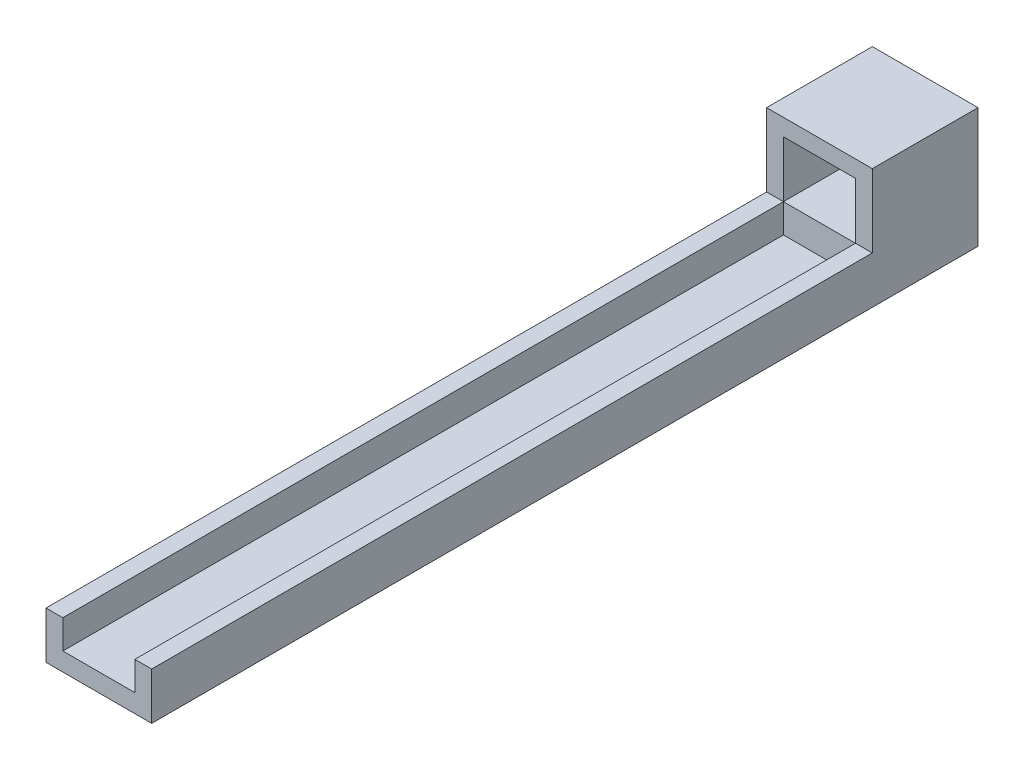
SolidWorks part; units mm, degrees
ref_plane "前基準面" through (0, 0, 0) normal (0, 0, 1) x (1, 0, 0)
ref_plane "上基準面" through (0, 0, 0) normal (0, 1, 0) x (1, 0, 0)
ref_plane "右基準面" through (0, 0, 0) normal (1, 0, 0) x (0, 0, -1)
sketch "草圖2" plane through (0, 0, 0) normal (0, 0, 1) x (1, 0, 0)
  line L1 (-25.6134, 5.4404) -> (-3.6134, 5.4404)
  line L2 (-25.6134, 5.4404) -> (-25.6134, -19.5596)
  line L3 (-25.6134, -19.5596) -> (-3.6134, -19.5596)
  line L4 (-3.6134, 5.4404) -> (-3.6134, -19.5596)
  line L5 (-22.1134, 1.9404) -> (-7.1134, 1.9404)
  line L6 (-22.1134, 1.9404) -> (-22.1134, -9.7596)
  line L7 (-22.1134, -9.7596) -> (-7.1134, -9.7596)
  line L8 (-7.1134, 1.9404) -> (-7.1134, -9.7596)
  dimension "D1" = 3.5
  dimension "D2" = 3.5
  dimension "D3" = 25
  dimension "D4" = 11.7
  dimension "D5" = 3.5
  dimension "D6" = 22
extrude "填料-伸長1" add sketch "草圖2" along normal blind 22
sketch "草圖3" plane through (0, 0, 22) normal (0, 0, 1) x (1, 0, 0)
  line L0 (-3.6134, -19.5596) -> (-3.6134, 5.4404) construction
  line L1 (-3.6134, -9.7596) -> (-25.6134, -9.7596)
  line L2 (-3.6134, -9.7596) -> (-3.6134, -19.5596)
  line L3 (-3.6134, -19.5596) -> (-25.6134, -19.5596)
  line L4 (-25.6134, -9.7596) -> (-25.6134, -19.5596)
  line L5 (-22.1134, -9.7596) -> (-7.1134, -9.7596) construction
  point P7 (-14.6134, -9.7596)
extrude "填料-伸長2" add sketch "草圖3" along normal blind 150
sketch "草圖4" plane through (0, -9.7596, 0) normal (0, 1, 0) x (1, 0, 0)
  line L0 (-3.6134, -172) -> (-25.6134, -172) construction
  line L1 (-7.1134, -172) -> (-22.1134, -172)
  line L2 (-7.1134, -172) -> (-7.1134, -22)
  line L3 (-7.1134, -22) -> (-22.1134, -22)
  line L4 (-22.1134, -172) -> (-22.1134, -22)
  line L5 (-3.6134, -22) -> (-25.6134, -22) construction
  line L6 (-25.6134, -172) -> (-25.6134, -22) construction
  line L7 (-3.6134, -172) -> (-3.6134, -22) construction
  dimension "D1" = 3.5
  dimension "D2" = 3.5
extrude "除料-伸長1" cut sketch "草圖4" against normal blind 6
ref_plane "平面1" through (-22.1134, -15.7596, 172) normal (1, 0, 0) x (0, 0, -1)
